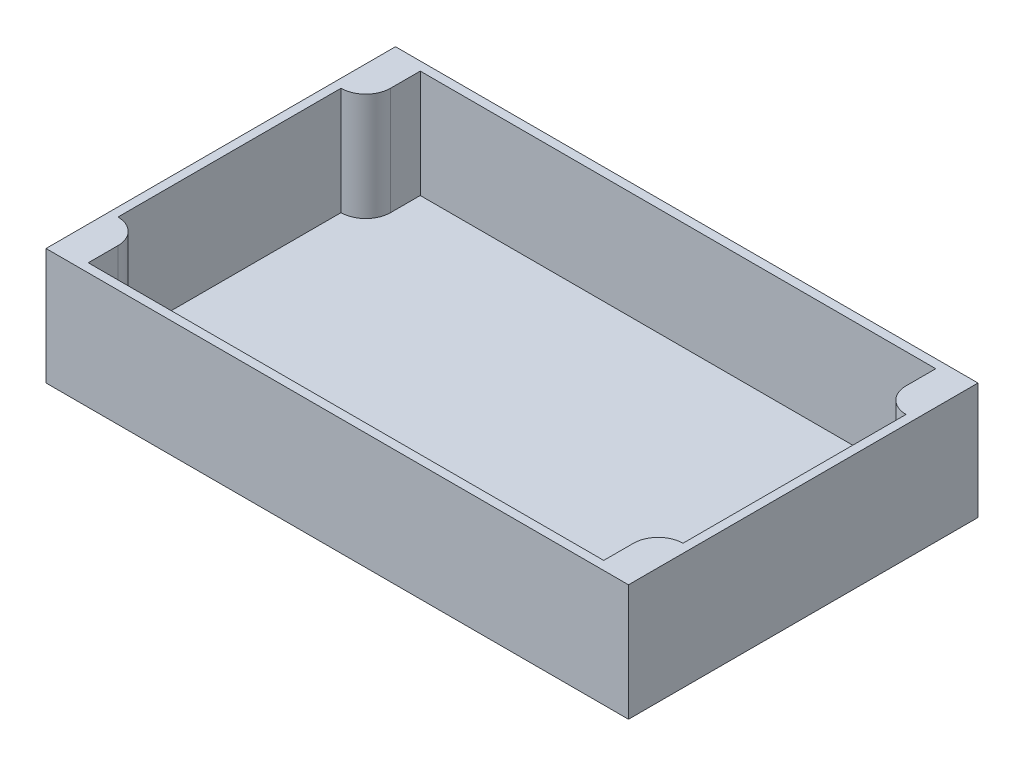
SolidWorks part; units mm, degrees
ref_plane "Front Plane" through (0, 0, 0) normal (0, 0, 1) x (1, 0, 0)
ref_plane "Top Plane" through (0, 0, 0) normal (0, 1, 0) x (1, 0, 0)
ref_plane "Right Plane" through (0, 0, 0) normal (1, 0, 0) x (0, 0, -1)
sketch "Sketch1" plane through (0, 0, 0) normal (0, 1, 0) x (1, 0, 0)
  line L1 (0, 0) -> (200, 0)
  line L2 (0, 0) -> (0, 120)
  line L3 (0, 120) -> (200, 120)
  line L4 (200, 0) -> (200, 120)
  dimension "D1" = 120
  dimension "D2" = 200
extrude "Boss-Extrude1" add sketch "Sketch1" along normal blind 3
sketch "Sketch2" plane through (0, 3, 0) normal (0, 1, 0) x (1, 0, 0)
  line L9 (0, 0) -> (0, 120)
  line L10 (0, 60) -> (3, 60) construction
  line L11 (3, 98.3) -> (3, 21.7)
  line L12 (11.5, 13.2) -> (11.5, 3)
  line L13 (0, 120) -> (0, 0) construction
  line L14 (0, 0) -> (200, 0) construction
  line L18 (11.5, 3) -> (188.5, 3)
  line L19 (100, 3) -> (100, 0) construction
  line L24 (200, 0) -> (0, 0)
  line L25 (100, 117) -> (100, 120) construction
  line L26 (200, 120) -> (0, 120)
  line L27 (11.5, 117) -> (188.5, 117)
  line L28 (11.5, 106.8) -> (11.5, 117)
  line L29 (200, 60) -> (197, 60) construction
  line L30 (188.5, 106.8) -> (188.5, 117)
  line L31 (188.5, 13.2) -> (188.5, 3)
  line L32 (197, 98.3) -> (197, 21.7)
  line L33 (200, 0) -> (200, 120)
  arc A4 (3, 21.7) -> (11.5, 13.2) centre (3, 13.2) cw
  arc A5 (3, 98.3) -> (11.5, 106.8) centre (3, 106.8) ccw
  arc A6 (197, 98.3) -> (188.5, 106.8) centre (197, 106.8) cw
  arc A7 (197, 21.7) -> (188.5, 13.2) centre (197, 13.2) ccw
  point P21 (0, 60)
  point P24 (100, 0)
  dimension "D1" = 3
  dimension "D2" = 8.5
  dimension "D3" = 18.7
extrude "Boss-Extrude2" add sketch "Sketch2" along direction (0, -1, 0) on the side of the normal offset from surface (37 mm away) 40
